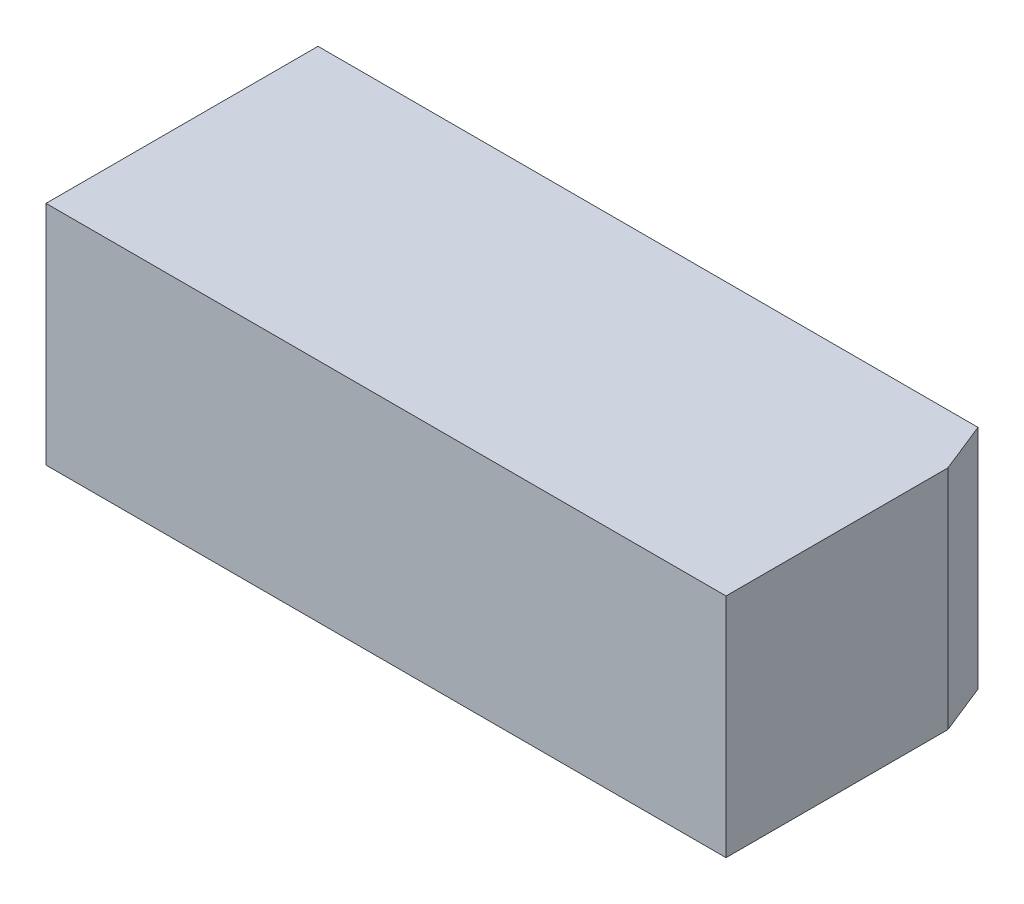
SolidWorks part; units mm, degrees
ref_plane "Front Plane" through (0, 0, 0) normal (0, 0, 1) x (1, 0, 0)
ref_plane "Top Plane" through (0, 0, 0) normal (0, 1, 0) x (1, 0, 0)
ref_plane "Right Plane" through (0, 0, 0) normal (1, 0, 0) x (0, 0, -1)
sketch "Sketch1" plane through (0, 0, 0) normal (0, 1, 0) x (1, 0, 0)
  line L1 (7.5, 3) -> (-7.5, 3)
  line L2 (7.5, 3) -> (7.5, -3)
  line L3 (7.5, -3) -> (-7.5, -3)
  line L4 (-7.5, 3) -> (-7.5, -3)
  line L5 (7.5, 3) -> (-7.5, -3) construction
  line L6 (7.5, -3) -> (-7.5, 3) construction
  point P0 (0, 0)
  dimension "D1" = 6
  dimension "D2" = 15
extrude "Main Body" add sketch "Sketch1" along normal blind 5
sketch "Sketch3" plane through (0, 0, 0) normal (0, -1, 0) x (1, 0, 0)
  line L0 (-7.5, -3) -> (-7.5, 3) construction
  line L1 (0, 0) -> (-4.5, 0) construction
  circle A0 centre (-4.5, 0) radius 1.25
  dimension "D1" = 2.5
  dimension "D2" = 3
extrude "GRIN Hole" cut sketch "Sketch3" against normal blind 4
sketch "Sketch2" plane through (0, 0, 0) normal (0, -1, 0) x (1, 0, 0)
  line L0 (-6.25, 1.875) -> (-6.25, -1.875) construction
  line L1 (2.5, 0) -> (-4.5, 0) construction
  line L2 (-4.5, 0) -> (-6.25, 0) construction
  circle A0 centre (-6.25, -1.875) radius 0.795
  circle A1 centre (-6.25, 1.875) radius 0.795
  circle A2 centre (2.5, 0) radius 0.795
  circle A3 centre (-4.5, 0) radius 1.25 construction
  dimension "D4" = 1.59
  dimension "D1" = 3.75
  dimension "D2" = 7
  dimension "D3" = 1.75
extrude "Magnet Holes" cut sketch "Sketch2" against normal blind 1
sketch "Sketch4" plane through (0, 0, 0) normal (0, -1, 0) x (1, 0, 0)
  line L0 (-7.5, 3) -> (7.5, -3) construction
  line L1 (7.5, 3) -> (7.5, -3) construction
  line L4 (7.5, -3) -> (-7.5, -3) construction
  line L5 (7.058, -3) -> (7.5, -1.8951)
  line L6 (7.5, -1.8951) -> (7.5, -3)
  line L7 (7.5, -3) -> (7.058, -3)
  dimension "D1" = 1.19
extrude "Set Screw Indent" cut sketch "Sketch4" against normal through all
